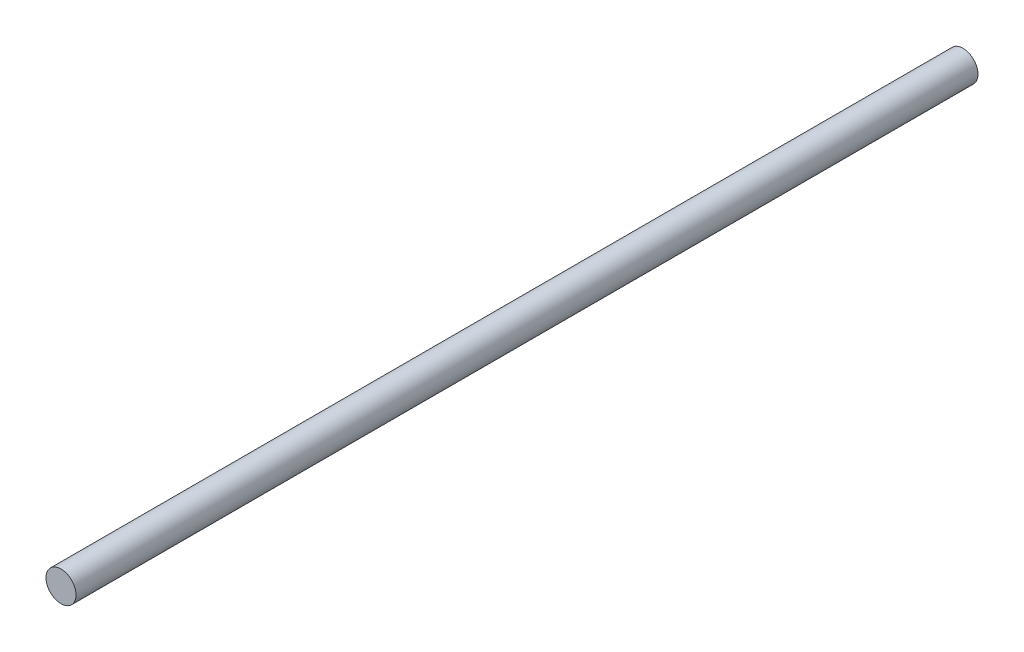
SolidWorks part; units mm, degrees
ref_plane "Спереди" through (0, 0, 0) normal (0, 0, 1) x (1, 0, 0)
ref_plane "Сверху" through (0, 0, 0) normal (0, 1, 0) x (1, 0, 0)
ref_plane "Справа" through (0, 0, 0) normal (1, 0, 0) x (0, 0, -1)
sketch "Эскиз1" plane through (0, 0, 0) normal (0, 0, 1) x (1, 0, 0)
  circle A0 centre (0, 0) radius 1.5
extrude "Бобышка-Вытянуть1" add sketch "Эскиз1" along normal blind 90
